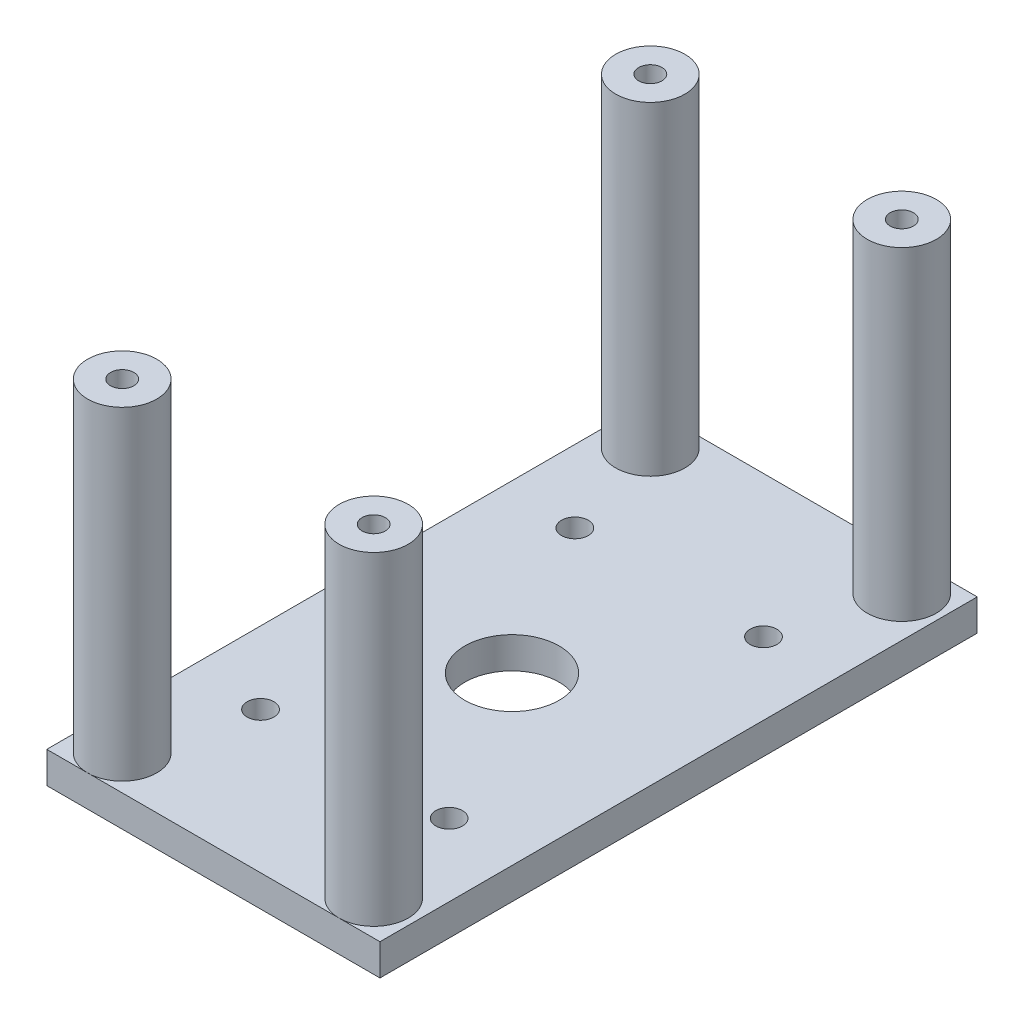
SolidWorks part; units mm, degrees
ref_plane "Front Plane" through (0, 0, 0) normal (0, 0, 1) x (1, 0, 0)
ref_plane "Top Plane" through (0, 0, 0) normal (0, 1, 0) x (1, 0, 0)
ref_plane "Right Plane" through (0, 0, 0) normal (1, 0, 0) x (0, 0, -1)
sketch "Sketch1" plane through (0, 0, 0) normal (0, 1, 0) x (1, 0, 0)
  line L1 (0, 0) -> (53, 0)
  line L2 (0, 0) -> (0, 95)
  line L3 (0, 95) -> (53, 95)
  line L4 (53, 0) -> (53, 95)
  dimension "D1" = 95
  dimension "D2" = 53
extrude "Boss-Extrude1" add sketch "Sketch1" along normal blind 5
sketch "Sketch2" plane through (0, 5, 0) normal (0, 1, 0) x (1, 0, 0)
  line L0 (53, 95) -> (0, 95) construction
  line L1 (0, 95) -> (0, 0) construction
  circle A0 centre (26.5, 47.5) radius 7.5 construction
  circle A1 centre (46.5, 89.5) radius 1.85
  circle A2 centre (6.5, 89.5) radius 1.85
  circle A3 centre (6.5, 5.5) radius 1.85
  circle A4 centre (46.5, 5.5) radius 1.85
  circle A5 centre (46.5, 89.5) radius 5.5
  circle A6 centre (6.5, 89.5) radius 5.5
  circle A7 centre (6.5, 5.5) radius 5.5
  circle A8 centre (46.5, 5.5) radius 5.5
  point P4 (26.5, 95)
  point P7 (0, 47.5)
  dimension "D1" = 15
  dimension "D2" = 42
  dimension "D5" = 3.7
  dimension "D6" = 40
  dimension "D7" = 11
  dimension "D3" = 20
  dimension "D4" = 84
extrude "Boss-Extrude2" add sketch "Sketch2" along normal blind 51.5
sketch "Sketch4" plane through (0, 5, 0) normal (0, 1, 0) x (1, 0, 0)
  line L1 (6.5, 0) -> (0, 0)
  circle A0 centre (26.5, 47.5) radius 7.5
  circle A1 centre (26.5, 47.5) radius 7.5 construction
  circle A2 centre (6.5, 5.5) radius 5.5 construction
  circle A4 centre (11.5, 72.5) radius 2.125
  circle A5 centre (41.5, 72.5) radius 2.125
  circle A6 centre (11.5, 22.5) radius 2.125
  circle A7 centre (41.5, 22.5) radius 2.125
  dimension "D1" = 4.25
  dimension "D2" = 30
  dimension "D3" = 15
  dimension "D4" = 50
  dimension "D5" = 25
extrude "Cut-Extrude1" cut sketch "Sketch4" against normal through all contours A0 | A4 | A5 | A6 | A7
